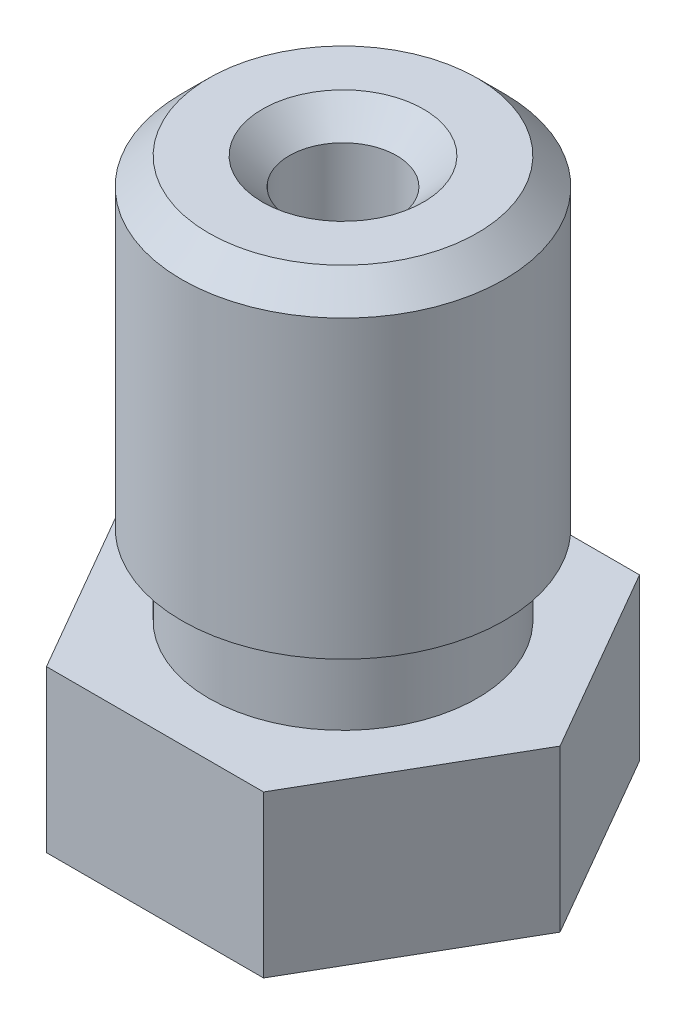
SolidWorks part; units mm, degrees
material "Brass"
ref_plane "Front Plane" through (0, 0, 0) normal (0, 0, 1) x (1, 0, 0)
ref_plane "Top Plane" through (0, 0, 0) normal (0, 1, 0) x (1, 0, 0)
ref_plane "Right Plane" through (0, 0, 0) normal (1, 0, 0) x (0, 0, -1)
ref_plane "Plane1" through (0, 0, 0) normal (0, -1, 0) x (1, 0, 0)
sketch "Sketch1" plane through (0, 0, 0) normal (0, -1, 0) x (1, 0, 0)
  line L0 (-2.0207, 3.5) -> (-4.0415, 0)
  line L1 (-4.0415, 0) -> (-2.0207, -3.5)
  line L2 (-2.0207, -3.5) -> (2.0207, -3.5)
  line L3 (2.0207, -3.5) -> (4.0415, 0)
  line L4 (4.0415, 0) -> (2.0207, 3.5)
  line L5 (2.0207, 3.5) -> (-2.0207, 3.5)
extrude "Boss-Extrude1" add sketch "Sketch1" against normal blind 3
ref_plane "Plane2" through (0, 0, 0) normal (0, 0, -1) x (-1, 0, 0)
sketch "Sketch2" plane through (0, 0, 0) normal (0, 0, -1) x (-1, 0, 0)
  line L0 (-2.5, 3) -> (0, 3)
  line L1 (0, 3) -> (0, 10.5)
  line L2 (0, 10.5) -> (-3, 10.5)
  line L3 (-3, 10.5) -> (-3, 4.5)
  line L4 (-3, 4.5) -> (-2.5, 4.5)
  line L5 (-2.5, 4.5) -> (-2.5, 3)
  line L6 (0, 3) -> (0, 10.5) construction
revolve "Revolve1" add sketch "Sketch2" angle 360 about L6
sketch "Sketch3" plane through (0, 0, 0) normal (0, 0, 1) x (1, 0, 0)
  line L0 (2.5, 0) -> (0, 0)
  line L1 (0, 0) -> (0, -2)
  line L2 (0, -2) -> (0.5, -2)
  line L3 (0.5, -2) -> (2.5, 0)
  line L4 (0, 0) -> (0, -2) construction
revolve "Revolve2" add sketch "Sketch3" angle 360 about L4
sketch "Sketch4" plane through (0, 0, 0) normal (0, 0, -1) x (-1, 0, 0)
  line L0 (-0.15, -2) -> (0, -2)
  line L1 (0, -2) -> (0, 10.5)
  line L2 (0, 10.5) -> (-1, 10.5)
  line L3 (-1, 10.5) -> (-1, 0)
  line L4 (-1, 0) -> (-0.75, -0.2273)
  line L5 (-0.75, -0.2273) -> (-0.75, -0.7)
  line L6 (-0.75, -0.7) -> (-0.15, -1.2)
  line L7 (-0.15, -1.2) -> (-0.15, -2)
  line L8 (0, -2) -> (0, 10.5) construction
  dimension "D1" = 1
  dimension "D2" = 0.15
  dimension "D3" = 0.75
  dimension "D4" = 0.5
  dimension "D5" = 0.8
  dimension "D6" = 0.2273
  dimension "D7" = 0.4727
revolve "Cut-Revolve1" cut sketch "Sketch4" angle 360 about L8
chamfer "Chamfer1" distance 0.5 angle 45 2 edges at (0, 10.5, 3) (0, 10.5, 1)
